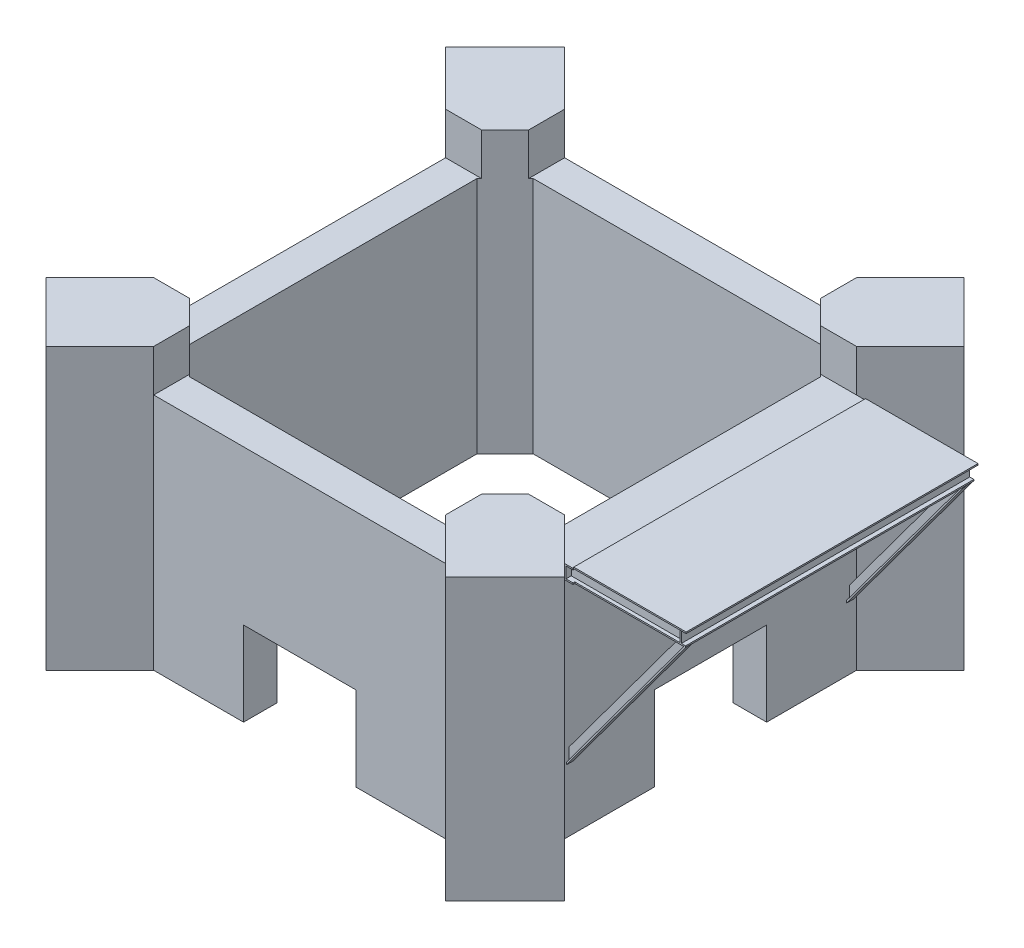
SolidWorks part; units mm, degrees
material "Portland High Strength Concrete"
ref_plane "Front Plane" through (0, 0, 0) normal (0, 0, 1) x (1, 0, 0)
ref_plane "Top Plane" through (0, 0, 0) normal (0, 1, 0) x (1, 0, 0)
ref_plane "Right Plane" through (0, 0, 0) normal (1, 0, 0) x (0, 0, -1)
sketch "Sketch1" plane through (0, 0, 0) normal (0, 1, 0) x (1, 0, 0)
  line L0 (-7121.3203, 5000) -> (-9242.6407, 7121.3203)
  line L5 (-7121.3203, 7121.3203) -> (7121.3203, -7121.3203) construction
  line L6 (-7121.3203, -7121.3203) -> (7121.3203, 7121.3203) construction
  line L7 (-7121.3203, 5000) -> (-5000, 7121.3203)
  line L8 (-9242.6407, 7121.3203) -> (-7121.3203, 9242.6407)
  line L9 (-5000, 7121.3203) -> (-7121.3203, 9242.6407)
  line L12 (7121.3203, 5000) -> (9242.6407, 7121.3203)
  line L13 (7121.3203, 5000) -> (5000, 7121.3203)
  line L14 (9242.6407, 7121.3203) -> (7121.3203, 9242.6407)
  line L15 (5000, 7121.3203) -> (7121.3203, 9242.6407)
  line L18 (0, 0) -> (7121.3203, 0) construction
  line L19 (7121.3203, -5000) -> (5000, -7121.3203)
  line L20 (5000, -7121.3203) -> (7121.3203, -9242.6407)
  line L21 (9242.6407, -7121.3203) -> (7121.3203, -9242.6407)
  line L22 (7121.3203, -5000) -> (9242.6407, -7121.3203)
  line L23 (-9242.6407, -7121.3203) -> (-7121.3203, -9242.6407)
  line L24 (-5000, -7121.3203) -> (-7121.3203, -9242.6407)
  line L25 (-7121.3203, -5000) -> (-5000, -7121.3203)
  line L26 (-7121.3203, -5000) -> (-9242.6407, -7121.3203)
  line L27 (5122.4478, 6122.4478) -> (6122.4478, 5122.4478)
  line L28 (-5122.4478, 6122.4478) -> (5122.4478, 6122.4478)
  line L29 (-6122.4478, 5122.4478) -> (-6122.4478, -5122.4478)
  line L30 (-5122.4478, -6122.4478) -> (5122.4478, -6122.4478)
  line L31 (6122.4478, 5122.4478) -> (6122.4478, -5122.4478)
  line L32 (-6122.4478, 6122.4478) -> (6122.4478, -6122.4478) construction
  line L33 (-6122.4478, -6122.4478) -> (6122.4478, 6122.4478) construction
  line L34 (5122.4478, -6122.4478) -> (6122.4478, -5122.4478)
  line L35 (-6122.4478, -5122.4478) -> (-5122.4478, -6122.4478)
  line L36 (-6122.4478, 5122.4478) -> (-5122.4478, 6122.4478)
  line L38 (-7322.4478, -7322.4478) -> (7322.4478, -7322.4478)
  line L39 (-7322.4478, -7322.4478) -> (-7322.4478, 7322.4478)
  line L40 (-7322.4478, 7322.4478) -> (7322.4478, 7322.4478)
  line L41 (7322.4478, -7322.4478) -> (7322.4478, 7322.4478)
  line L42 (-7322.4478, -7322.4478) -> (7322.4478, 7322.4478) construction
  line L43 (-7322.4478, 7322.4478) -> (7322.4478, -7322.4478) construction
  point P0 (0, 0)
  dimension "D1" = 3000
  dimension "D2" = 14242.6407
  dimension "D3" = 3000
  dimension "D4" = 12244.8955
  dimension "D5" = 18485.2814
  dimension "D6" = 45
  dimension "D7" = 10244.8955
  dimension "D8" = 6122.4478
  dimension "D9" = 1200
extrude "Boss-Extrude1" add sketch "Sketch1" along normal blind 10000
sketch "Sketch4" plane through (0, 10000, 0) normal (0, 1, 0) x (1, 0, 0)
  line L0 (-5201.1274, -5201.1274) -> (-5201.1274, -7322.4478)
  line L1 (-7322.4478, 5201.1274) -> (-5201.1274, 5201.1274)
  line L2 (-7322.4478, 5201.1274) -> (-7322.4478, -5201.1274)
  line L3 (-7322.4478, -5201.1274) -> (-5201.1274, -5201.1274)
  line L4 (7322.4478, 5201.1274) -> (7322.4478, -5201.1274)
  line L5 (5201.1274, 7322.4478) -> (-5201.1274, 7322.4478)
  line L6 (5201.1274, 7322.4478) -> (5201.1274, 5201.1274)
  line L7 (5201.1274, -7322.4478) -> (-5201.1274, -7322.4478)
  line L8 (-5201.1274, 7322.4478) -> (-5201.1274, 5201.1274)
  line L9 (5201.1274, 5201.1274) -> (7322.4478, 5201.1274)
  line L10 (5201.1274, -5201.1274) -> (7322.4478, -5201.1274)
  line L11 (5201.1274, -5201.1274) -> (5201.1274, -7322.4478)
extrude "Cut-Extrude3" cut sketch "Sketch4" against normal blind 1500
sketch "Sketch5" plane through (0, 0, 7322.4478) normal (0, 0, 1) x (1, 0, 0)
  line L0 (-5201.1274, 0) -> (5201.1274, 0) construction
  line L1 (-2000, 0) -> (2000, 0)
  line L2 (-2000, 0) -> (-2000, 3000)
  line L3 (-2000, 3000) -> (2000, 3000)
  line L4 (2000, 0) -> (2000, 3000)
  line L5 (0, 0) -> (0, 3000) construction
  dimension "D1" = 3000
  dimension "D2" = 4000
extrude "Cut-Extrude4" cut sketch "Sketch5" against normal blind 1353
sketch "Sketch6" plane through (7322.4478, 0, 0) normal (1, 0, 0) x (0, 0, -1)
  line L0 (-5201.1274, 0) -> (5201.1274, 0) construction
  line L1 (-2000, 0) -> (2000, 0)
  line L2 (-2000, 0) -> (-2000, 3000)
  line L3 (-2000, 3000) -> (2000, 3000)
  line L4 (2000, 0) -> (2000, 3000)
  line L5 (0, 3000) -> (0, 0) construction
  dimension "D1" = 3000
  dimension "D2" = 4000
extrude "Cut-Extrude5" cut sketch "Sketch6" against normal blind 1353
sketch "Sketch7" plane through (7322.4478, 0, 0) normal (1, 0, 0) x (0, 0, -1)
  line L0 (0, 0) -> (0, 8500) construction
  line L1 (-5201.1274, 8500) -> (5201.1274, 8500) construction
  line L2 (-5201.1274, 8500) -> (-5201.1274, 8000)
  line L3 (-5201.1274, 8500) -> (-5201.1274, 0) construction
  line L4 (-5201.1274, 8000) -> (5201.1274, 8000)
  line L5 (5201.1274, 8500) -> (5201.1274, 0) construction
  line L6 (5201.1274, 8000) -> (5201.1274, 8500)
  line L7 (5201.1274, 8500) -> (-5201.1274, 8500)
  dimension "D1" = 500
extrude "Boss-Extrude2" add sketch "Sketch7" along normal blind 50
sketch "Sketch8" plane through (7372.4478, 0, 0) normal (1, 0, 0) x (0, 0, -1)
  line L0 (5201.1274, 8500) -> (5201.1274, 8000) construction
  line L1 (-5201.1274, 8500) -> (5201.1274, 8500)
  line L2 (-5201.1274, 8500) -> (-5201.1274, 8450)
  line L3 (-5201.1274, 8450) -> (5201.1274, 8450)
  line L4 (5201.1274, 8500) -> (5201.1274, 8450)
  line L5 (-5201.1274, 8500) -> (-5201.1274, 8000) construction
  line L6 (5201.1274, 8000) -> (-5201.1274, 8000)
  line L7 (5201.1274, 8000) -> (5201.1274, 8050)
  line L8 (5201.1274, 8050) -> (-5201.1274, 8050)
  line L9 (-5201.1274, 8000) -> (-5201.1274, 8050)
  dimension "D1" = 50
extrude "Boss-Extrude3" add sketch "Sketch8" along normal blind 250
sketch "Sketch9" plane through (7372.4478, 0, 0) normal (1, 0, 0) x (0, 0, -1)
  line L1 (-5013.6274, 8450) -> (-4963.6274, 8450)
  line L3 (-5013.6274, 8050) -> (-4963.6274, 8050)
  line L12 (-5013.6274, 8450) -> (-5013.6274, 8050)
  line L13 (-4963.6274, 8050) -> (-4963.6274, 8450)
  line L14 (-4988.6274, 8050) -> (-4988.6274, 8450) construction
  line L15 (-5201.1274, 8450) -> (5201.1274, 8450) construction
  line L16 (5201.1274, 8050) -> (-5201.1274, 8050) construction
  line L17 (0, 8000) -> (0, 8500) construction
  line L18 (-5201.1274, 8000) -> (5201.1274, 8000) construction
  line L19 (5201.1274, 8500) -> (-5201.1274, 8500) construction
  line L20 (4988.6274, 8050) -> (4988.6274, 8450) construction
  line L21 (4963.6274, 8050) -> (4963.6274, 8450)
  line L22 (5013.6274, 8450) -> (5013.6274, 8050)
  line L23 (5013.6274, 8050) -> (4963.6274, 8050)
  line L24 (5013.6274, 8450) -> (4963.6274, 8450)
  line L25 (-4963.6274, 8250) -> (-25, 8250) construction
  line L26 (-25, 8450) -> (25, 8450)
  line L27 (-25, 8450) -> (-25, 8050)
  line L28 (-25, 8050) -> (25, 8050)
  line L29 (25, 8450) -> (25, 8050)
  line L30 (-2507.4139, 8450) -> (-2507.4139, 8050) construction
  line L31 (-5201.1274, 8450) -> (5201.1274, 8450) construction
  line L32 (5201.1274, 8050) -> (-5201.1274, 8050) construction
  line L33 (25, 8250) -> (4963.6274, 8250) construction
  line L34 (2504.0386, 8450) -> (2504.0386, 8050) construction
  line L36 (2479.0386, 8450) -> (2529.0386, 8450)
  line L37 (2479.0386, 8450) -> (2479.0386, 8050)
  line L38 (2479.0386, 8050) -> (2529.0386, 8050)
  line L39 (2529.0386, 8450) -> (2529.0386, 8050)
  line L40 (-2532.4139, 8450) -> (-2482.4139, 8450)
  line L41 (-2532.4139, 8450) -> (-2532.4139, 8050)
  line L42 (-2532.4139, 8050) -> (-2482.4139, 8050)
  line L43 (-2482.4139, 8450) -> (-2482.4139, 8050)
  dimension "D1" = 50
  dimension "D2" = 25
  dimension "D3" = 50
  dimension "D4" = 25
  dimension "D5" = 25
  dimension "D6" = 50
  dimension "D7" = 25
  dimension "D8" = 50
extrude "Boss-Extrude4" add sketch "Sketch9" along normal blind 4000
sketch "Sketch10" plane through (0, 8450, 0) normal (0, 1, 0) x (1, 0, 0)
  line L0 (7622.4478, 5201.1274) -> (7622.4478, -5201.1274) construction
  line L1 (7622.4478, 5138.6274) -> (11222.4478, 5138.6274)
  line L2 (7622.4478, 5138.6274) -> (7622.4478, 4838.6274)
  line L3 (7622.4478, 4838.6274) -> (11222.4478, 4838.6274)
  line L4 (11222.4478, 5138.6274) -> (11222.4478, 4838.6274)
  line L5 (11372.4478, -5013.6274) -> (7622.4478, -5013.6274) construction
  line L6 (7622.4478, 2654.0386) -> (11222.4478, 2654.0386)
  line L7 (7622.4478, 2654.0386) -> (7622.4478, 2354.0386)
  line L8 (7622.4478, 2354.0386) -> (11222.4478, 2354.0386)
  line L9 (11222.4478, 2654.0386) -> (11222.4478, 2354.0386)
  line L10 (7622.4478, 150) -> (11222.4478, 150)
  line L11 (7622.4478, 150) -> (7622.4478, -150)
  line L12 (7622.4478, -150) -> (11222.4478, -150)
  line L13 (11222.4478, 150) -> (11222.4478, -150)
  line L14 (7622.4478, -2357.4139) -> (11222.4478, -2357.4139)
  line L15 (7622.4478, -2357.4139) -> (7622.4478, -2657.4139)
  line L16 (7622.4478, -2657.4139) -> (11222.4478, -2657.4139)
  line L17 (11222.4478, -2357.4139) -> (11222.4478, -2657.4139)
  line L18 (7622.4478, -4838.6274) -> (11222.4478, -4838.6274)
  line L19 (7622.4478, -4838.6274) -> (7622.4478, -5138.6274)
  line L20 (7622.4478, -5138.6274) -> (11222.4478, -5138.6274)
  line L21 (11222.4478, -4838.6274) -> (11222.4478, -5138.6274)
  line L22 (11372.4478, -4963.6274) -> (11372.4478, -5013.6274) construction
  line L23 (11372.4478, -2532.4139) -> (7622.4478, -2532.4139) construction
  line L24 (11372.4478, -25) -> (7622.4478, -25) construction
  line L25 (11372.4478, 2479.0386) -> (7622.4478, 2479.0386) construction
  line L26 (11372.4478, 4963.6274) -> (7622.4478, 4963.6274) construction
  dimension "D1" = 300
  dimension "D2" = 125
  dimension "D3" = 150
  dimension "D4" = 125
  dimension "D5" = 125
  dimension "D6" = 125
  dimension "D7" = 125
extrude "Boss-Extrude5" add sketch "Sketch10" along normal blind 50
sketch "Sketch11" plane through (0, 8050, 0) normal (0, -1, 0) x (1, 0, 0)
  line L0 (11222.4478, -5138.6274) -> (7622.4478, -5138.6274) construction
  line L1 (7622.4478, -4838.6274) -> (11222.4478, -4838.6274) construction
  line L2 (11222.4478, -2654.0386) -> (7622.4478, -2654.0386) construction
  line L3 (7622.4478, -2354.0386) -> (11222.4478, -2354.0386) construction
  line L4 (11222.4478, -150) -> (7622.4478, -150) construction
  line L5 (7622.4478, 150) -> (11222.4478, 150) construction
  line L6 (11222.4478, 2357.4139) -> (7622.4478, 2357.4139) construction
  line L7 (7622.4478, 2657.4139) -> (11222.4478, 2657.4139) construction
  line L8 (11222.4478, 4838.6274) -> (7622.4478, 4838.6274) construction
  line L9 (7622.4478, 5138.6274) -> (11222.4478, 5138.6274) construction
  line L10 (11222.4478, -5138.6274) -> (7622.4478, -5138.6274)
  line L11 (7622.4478, -4838.6274) -> (11222.4478, -4838.6274)
  line L12 (11222.4478, -2654.0386) -> (7622.4478, -2654.0386)
  line L13 (7622.4478, -2354.0386) -> (11222.4478, -2354.0386)
  line L14 (11222.4478, -150) -> (7622.4478, -150)
  line L15 (7622.4478, 150) -> (11222.4478, 150)
  line L16 (11222.4478, 2357.4139) -> (7622.4478, 2357.4139)
  line L17 (7622.4478, 2657.4139) -> (11222.4478, 2657.4139)
  line L18 (11222.4478, 4838.6274) -> (7622.4478, 4838.6274)
  line L19 (7622.4478, 5138.6274) -> (11222.4478, 5138.6274)
  line L20 (7622.4478, -5138.6274) -> (7622.4478, -4838.6274)
  line L21 (11222.4478, 5138.6274) -> (11222.4478, 4838.6274)
  line L22 (11222.4478, -4838.6274) -> (11222.4478, -5138.6274)
  line L23 (7622.4478, -2654.0386) -> (7622.4478, -2354.0386)
  line L24 (11222.4478, -2354.0386) -> (11222.4478, -2654.0386)
  line L25 (7622.4478, -150) -> (7622.4478, 150)
  line L26 (11222.4478, 150) -> (11222.4478, -150)
  line L27 (7622.4478, 2357.4139) -> (7622.4478, 2657.4139)
  line L28 (11222.4478, 2657.4139) -> (11222.4478, 2357.4139)
  line L29 (7622.4478, 4838.6274) -> (7622.4478, 5138.6274)
extrude "Boss-Extrude6" add sketch "Sketch11" along normal blind 50
sketch "Sketch12" plane through (11372.4478, 0, 0) normal (1, 0, 0) x (0, 0, -1)
  line L1 (-5138.6274, 8450) -> (5138.6274, 8450)
  line L2 (-5138.6274, 8450) -> (-5138.6274, 8050)
  line L3 (-5138.6274, 8050) -> (5138.6274, 8050)
  line L4 (5138.6274, 8450) -> (5138.6274, 8050)
extrude "Boss-Extrude7" add sketch "Sketch12" along normal blind 50
sketch "Sketch13" plane through (0, 8450, 0) normal (0, 1, 0) x (1, 0, 0)
  line L1 (11222.4478, 5138.6274) -> (11572.4478, 5138.6274)
  line L2 (11222.4478, 5138.6274) -> (11222.4478, -5138.6274)
  line L3 (11222.4478, -5138.6274) -> (11572.4478, -5138.6274)
  line L4 (11572.4478, 5138.6274) -> (11572.4478, -5138.6274)
  line L5 (11422.4478, 5138.6274) -> (11422.4478, -5138.6274) construction
  point P4 (10222.4478, -5138.6274)
  dimension "D1" = 150
extrude "Boss-Extrude8" add sketch "Sketch13" along normal blind 50
sketch "Sketch15" plane through (0, 8500, 0) normal (0, 1, 0) x (1, 0, 0)
  line L0 (7622.4478, 5201.1274) -> (11655.106, 5201.1274) construction
  line L1 (11655.106, 5201.1274) -> (7646.9514, 5201.1274)
  line L2 (11655.106, 5201.1274) -> (11655.106, -5201.1274)
  line L3 (11655.106, -5201.1274) -> (7646.9514, -5201.1274)
  line L4 (7646.9514, 5201.1274) -> (7646.9514, -5201.1274)
  line L5 (7622.4478, -5201.1274) -> (7646.9514, -5201.1274) construction
extrude "Boss-Extrude11" add sketch "Sketch15" along normal blind 50
sketch "Sketch14" plane through (0, 8050, 0) normal (0, -1, 0) x (1, 0, 0)
  line L0 (11372.4478, -5138.6274) -> (7622.4478, -5138.6274) construction
  line L1 (11572.4478, 5138.6274) -> (11222.4478, 5138.6274)
  line L2 (11572.4478, 5138.6274) -> (11572.4478, -5138.6274)
  line L3 (11572.4478, -5138.6274) -> (11222.4478, -5138.6274)
  line L4 (11222.4478, 5138.6274) -> (11222.4478, -5138.6274)
  point P4 (11801.9117, -5120.89)
  point P5 (10226.6409, -5138.6274)
  point P9 (11222.4478, -5138.6274)
extrude "Boss-Extrude9" add sketch "Sketch14" along normal blind 50
ref_plane "Plane1" through (0, 0, 5000) normal (0, 0, 1) x (1, 0, 0)
ref_plane "Plane2" through (0, 0, -5000) normal (0, 0, 1) x (1, 0, 0)
sketch "Sketch16" plane through (0, 0, 5000) normal (0, 0, 1) x (1, 0, 0)
  line L0 (11572.4478, 8000) -> (7302.6006, 2224.4059)
  line L1 (11199.3664, 8000) -> (7302.6006, 2729.053)
  line L2 (11572.4478, 8000) -> (7622.4478, 8000) construction
  line L3 (11199.3664, 8000) -> (11572.4478, 8000)
  line L4 (7302.6006, 2729.053) -> (7302.6006, 2224.4059)
  dimension "D1" = 300
extrude "Boss-Extrude12" add sketch "Sketch16" along normal blind 50
sketch "Sketch17" plane through (3658.5366, -2704.7247, 0) normal (0.8041, -0.5945, 0) x (0, 0, -1)
  line L1 (-5138.6274, 13314.9957) -> (-4900, 13314.9957)
  line L2 (-5138.6274, 13314.9957) -> (-5138.6274, 6130.5055)
  line L3 (-5138.6274, 6130.5055) -> (-4900, 6130.5055)
  line L4 (-4900, 13314.9957) -> (-4900, 6130.5055)
  line L6 (-5000, 6163.2744) -> (-5000, 13312.4423) construction
  point P7 (0, 0)
  point P8 (0, 0)
  dimension "D1" = 100
extrude "Boss-Extrude17" add sketch "Sketch17" against normal blind 50
sketch "Sketch18" plane through (0, 0, -5000) normal (0, 0, 1) x (1, 0, 0)
  line L0 (11199.3664, 8000) -> (7302.6006, 2729.053) construction
  line L1 (7302.6006, 2729.053) -> (7302.6006, 2224.4059) construction
  line L2 (11572.4478, 8000) -> (7302.6006, 2224.4059) construction
  line L3 (11199.3664, 8000) -> (11572.4478, 8000) construction
  line L4 (11199.3664, 8000) -> (7302.6006, 2729.053)
  line L5 (7302.6006, 2729.053) -> (7302.6006, 2224.4059)
  line L6 (11572.4478, 8000) -> (7302.6006, 2224.4059)
  line L7 (11199.3664, 8000) -> (11572.4478, 8000)
extrude "Boss-Extrude18" add sketch "Sketch18" along normal blind 50
sketch "Sketch19" plane through (3658.5366, -2704.7247, 0) normal (0.8041, -0.5945, 0) x (0, 0, -1)
  line L0 (4950, 6569.0684) -> (4950, 6163.2744) construction
  line L1 (4850, 13312.4423) -> (5100, 13312.4423)
  line L2 (4850, 13312.4423) -> (4850, 6090.3873)
  line L3 (4850, 6090.3873) -> (5100, 6090.3873)
  line L4 (5100, 13312.4423) -> (5100, 6090.3873)
  line L5 (5138.6274, 13312.4423) -> (5000, 13312.4423) construction
  point P6 (5100, 13312.4423)
  point P9 (0, 0)
  dimension "D1" = 100
  dimension "D2" = 250
extrude "Boss-Extrude20" add sketch "Sketch19" against normal blind 50
